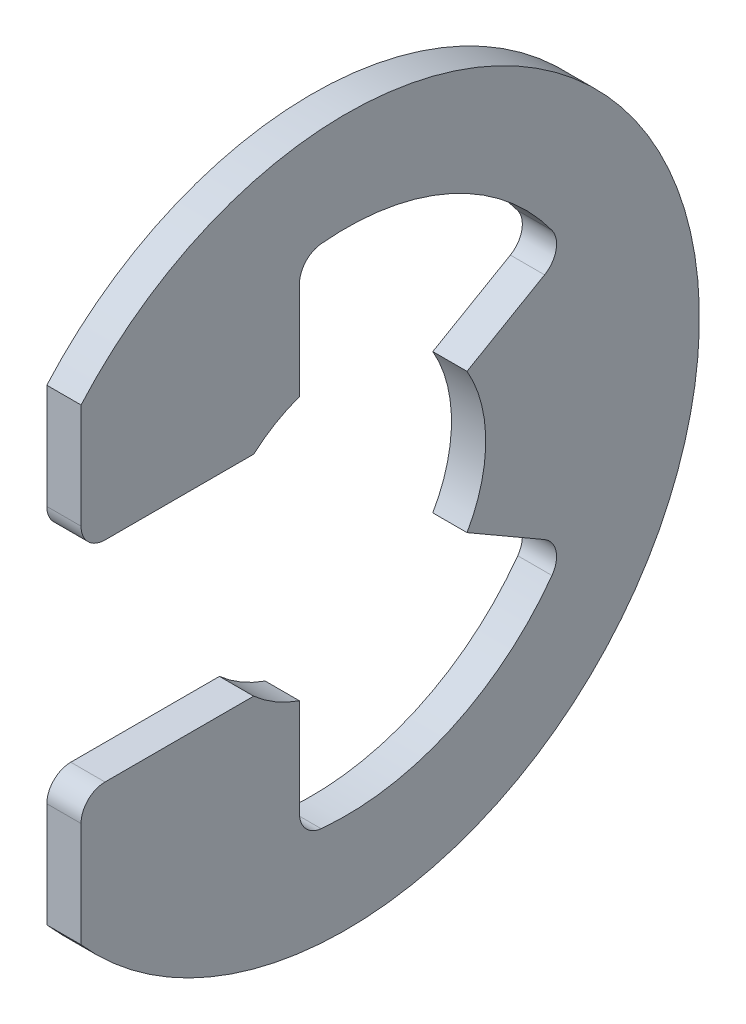
SolidWorks part; units mm, degrees
material "Plain Carbon Steel"
ref_plane "Front" through (0, 0, 0) normal (0, 0, 1) x (1, 0, 0)
ref_plane "Top" through (0, 0, 0) normal (0, 1, 0) x (1, 0, 0)
ref_plane "Right" through (0, 0, 0) normal (1, 0, 0) x (0, 0, -1)
sketch "Sketch1" plane through (0, 0, 0) normal (1, 0, 0) x (0, 0, -1)
  line L0 (-1.7137, 1.9431) -> (-4.9149, 1.9431)
  line L1 (-4.9149, 4.3345) -> (-4.9149, 1.9431)
  line L2 (-4.9149, -4.3345) -> (-4.9149, -1.9431)
  line L3 (-4.9149, -1.9431) -> (-1.7137, -1.9431)
  line L4 (2.2437, -1.2954) -> (4.0872, -2.3597)
  line L5 (2.2437, 1.2954) -> (4.0872, 2.3597)
  line L6 (0, 0) -> (-6.731, 0) construction
  line L7 (2.2437, 1.2954) -> (2.2437, -1.2954) construction
  line L8 (-0.8636, -2.4426) -> (-0.8636, -4.6398)
  line L9 (0, 6.5532) -> (0, -6.5532) construction
  line L10 (-0.8636, 4.6398) -> (-0.8636, 2.4426)
  circle A1 centre (0, 0) radius 6.731 construction
  circle A2 centre (0, 0) radius 2.5908 construction
  arc A3 (-4.9149, -4.3345) -> (-4.9149, 4.3345) centre (0, 0) ccw
  arc A4 (-1.7137, -1.9431) -> (-0.8636, -2.4426) centre (0, 0) ccw
  arc A5 (-1.7137, 1.9431) -> (-0.8636, 2.4426) centre (0, 0) cw
  arc A6 (2.2437, 1.2954) -> (2.2437, -1.2954) centre (0, 0) cw
  arc A7 (-0.8636, -4.6398) -> (4.0872, -2.3597) centre (0, 0) ccw
  arc A8 (4.0872, 2.3597) -> (-0.8636, 4.6398) centre (0, 0) ccw
  dimension "D1" = 4.7195
  dimension "OD" = 13.1064
  dimension "L" = 13.462
  dimension "D" = 5.1816
  dimension "D5" = 0.8636
  dimension "D2" = 60
  dimension "D3" = 3.8862
  dimension "D4" = 11.4681
extrude "Extrude1" add sketch "Sketch1" along normal mid plane 0.635
fillet "Fillet1" radius 0.4445 6 edges at (0, -2.3597, -4.0872) (0, 2.3597, -4.0872) (0, -1.9431, 4.9149) (0, -4.6398, 0.8636) (0, 1.9431, 4.9149) (0, 4.6398, 0.8636)
sketch "Sketch3" plane through (0, 0, 0) normal (0, 1, 0) x (1, 0, 0)
  line L0 (0.3683, 3.175) -> (0.3683, 2.667)
  line L1 (0.3683, 2.667) -> (-0.3683, 2.667)
  line L2 (-0.3683, 2.667) -> (-0.3683, 3.175)
  line L3 (-0.3683, 3.175) -> (-5.1562, 3.175)
  line L4 (2.2098, 0) -> (2.2098, 2.921)
  line L5 (-5.1562, 3.175) -> (-5.1562, 0)
  line L6 (-5.1562, 0) -> (2.2098, 0)
  line L8 (2.2098, 0) -> (2.2098, 3.175) construction
  line L9 (2.2098, 3.175) -> (0.3683, 3.175) construction
  line L10 (2.2098, 0) -> (17.2631, 0) construction
  line L11 (2.2098, 2.921) -> (1.9558, 3.175)
  line L12 (1.9558, 3.175) -> (0.3683, 3.175)
  point P2 (0, 2.667)
  point P5 (0.3683, 2.921)
  dimension "D1" = 1.8415
  dimension "Ds" = 6.35
  dimension "Dg" = 5.334
  dimension "W" = 0.7366
  dimension "D2" = 7.366
  dimension "D3" = 45
revolve "Revolve2" [suppressed] add sketch "Sketch3" angle 360 about L10
equation "\"D2@Sketch3\" = \"W@Sketch3\"*10"
equation "\"D1@Sketch3\" = \"D2@Sketch3\"/4"
equation "\"D1@Sketch1\" = (\"OD@Sketch1\"+\"D@Sketch1\")/3.875"
equation "\"D3@Sketch1\" = \"D@Sketch1\"*.75"
equation "\"D1@Fillet1\" = \"D1@Extrude1\"*.7"
equation "\"D4@Sketch1\" = \"OD@Sketch1\"*.875"
equation "\"D5@Sketch1\" = \"D@Sketch1\"/6"
